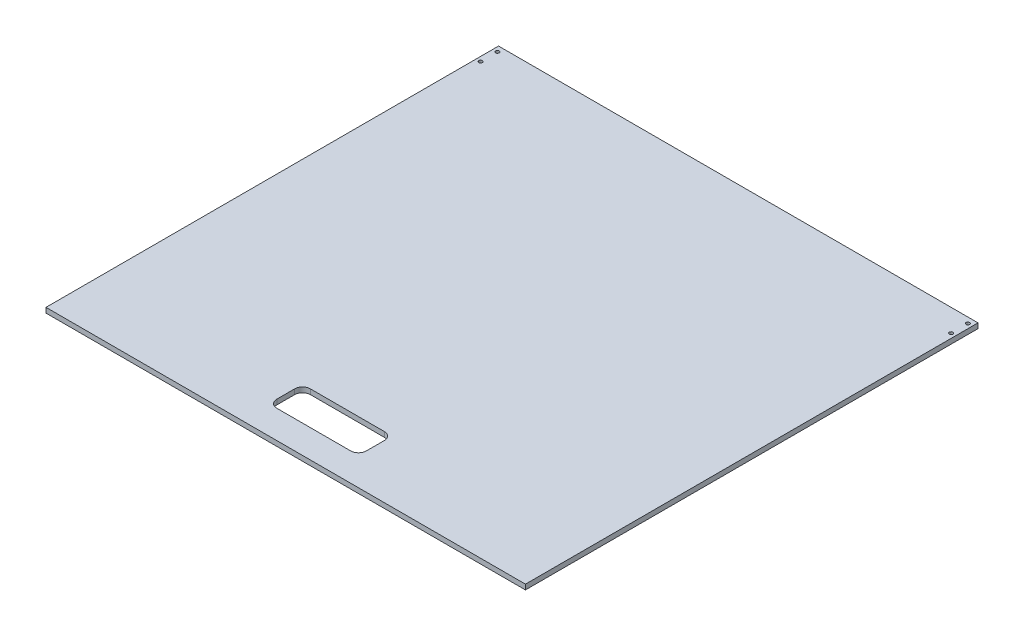
SolidWorks part; units mm, degrees
ref_plane "Front Plane" through (0, 0, 0) normal (0, 0, 1) x (1, 0, 0)
ref_plane "Top Plane" through (0, 0, 0) normal (0, 1, 0) x (1, 0, 0)
ref_plane "Right Plane" through (0, 0, 0) normal (1, 0, 0) x (0, 0, -1)
sketch "Sketch1" plane through (0, 0, 0) normal (0, 1, 0) x (1, 0, 0)
  line L1 (-214, -202) -> (214, -202)
  line L2 (-214, -202) -> (-214, 202)
  line L3 (-214, 202) -> (214, 202)
  line L4 (214, -202) -> (214, 202)
  line L5 (-214, -202) -> (214, 202) construction
  line L6 (-214, 202) -> (214, -202) construction
  point P0 (0, 0)
  dimension "D1" = 428
  dimension "D2" = 404
extrude "Boss-Extrude1" add sketch "Sketch1" along normal blind 4.5
sketch "Sketch2" plane through (0, 0, 0) normal (0, -1, 0) x (1, 0, 0)
  line L0 (214, -202) -> (-214, -202) construction
  line L1 (214, 202) -> (214, -202) construction
  circle A0 centre (210, -182) radius 1.6
  circle A1 centre (210, -197) radius 1.6
  dimension "D1" = 5
  dimension "D3" = 3.2
  dimension "D2" = 15
  dimension "D4" = 4
extrude "Cut-Extrude1" cut sketch "Sketch2" against normal through all
mirror "Mirror1" about plane through (0, 0, 0) normal (1, 0, 0) of "Cut-Extrude1"
sketch "Sketch3" plane through (0, 4.5, 0) normal (0, 1, 0) x (1, 0, 0)
  line L0 (-214, -202) -> (214, -202) construction
  line L1 (-33, -177) -> (33, -177)
  line L2 (-40, -170) -> (-40, -154)
  line L3 (-33, -147) -> (33, -147)
  line L4 (40, -170) -> (40, -154)
  line L5 (-40, -177) -> (40, -147) construction
  line L6 (-40, -147) -> (40, -177) construction
  arc A0 (-40, -154) -> (-33, -147) centre (-33, -154) cw
  arc A1 (-33, -177) -> (-40, -170) centre (-33, -170) cw
  arc A2 (33, -177) -> (40, -170) centre (33, -170) ccw
  arc A3 (33, -147) -> (40, -154) centre (33, -154) cw
  point P0 (0, -162)
  dimension "D4" = 7
  dimension "D1" = 25
  dimension "D2" = 80
  dimension "D3" = 30
extrude "Cut-Extrude2" cut sketch "Sketch3" against normal through all
